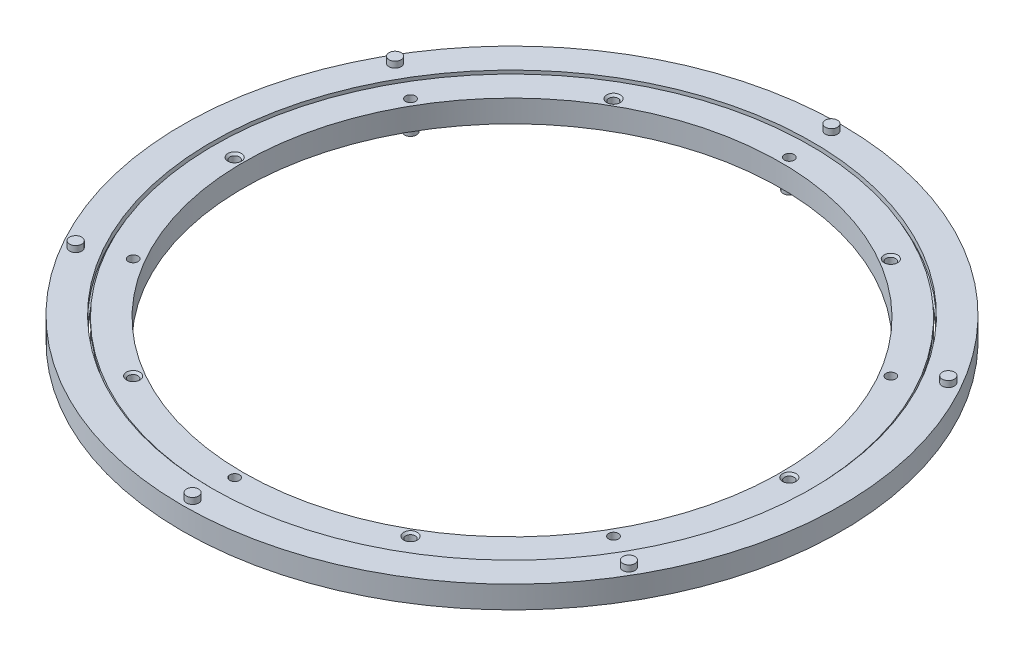
SolidWorks part; units mm, degrees
ref_plane "Front Plane" through (0, 0, 0) normal (0, 0, 1) x (1, 0, 0)
ref_plane "Top Plane" through (0, 0, 0) normal (0, 1, 0) x (1, 0, 0)
ref_plane "Right Plane" through (0, 0, 0) normal (1, 0, 0) x (0, 0, -1)
sketch "Sketch1" plane through (0, 0, 0) normal (0, 1, 0) x (1, 0, 0)
  line L0 (0, 162.5) -> (0, -162.5) construction
  line L1 (-162.5, 0) -> (162.5, 0) construction
  line L2 (68.375, 118.429) -> (0, 0) construction
  circle A0 centre (0, 0) radius 132.5
  circle A1 centre (0, 0) radius 162.5
  circle A2 centre (0, 0) radius 157.5 construction
  circle A3 centre (0, 0) radius 136.75 construction
  circle A4 centre (0, 157.5) radius 3
  circle A5 centre (0, 157.5) radius 2.4
  circle A6 centre (0, 136.75) radius 2.4
  circle A7 centre (0, 136.75) radius 3
  circle A8 centre (136.399, 78.75) radius 2.4
  circle A9 centre (136.399, -78.75) radius 2.4
  circle A10 centre (0, -157.5) radius 2.4
  circle A11 centre (-136.399, -78.75) radius 2.4
  circle A12 centre (-136.399, 78.75) radius 2.4
  circle A17 centre (118.429, 68.375) radius 2.4
  circle A18 centre (118.429, -68.375) radius 2.4
  circle A19 centre (0, -136.75) radius 2.4
  circle A20 centre (-118.429, -68.375) radius 2.4
  circle A21 centre (-118.429, 68.375) radius 2.4
  circle A24 centre (68.375, 118.429) radius 2.35
  circle A25 centre (136.75, 0) radius 2.35
  circle A26 centre (68.375, -118.429) radius 2.35
  circle A27 centre (-68.375, -118.429) radius 2.35
  circle A52 centre (-136.75, 0) radius 2.35
  circle A53 centre (-68.375, 118.429) radius 2.35
  point P28 (69.55, 120.4641)
  point P36 (0, 0)
  point P38 (0, 132.5)
  point P39 (0, 159.9)
  point P51 (0, 0)
  point P52 (0, 160.5)
  point P61 (0, 0)
  point P62 (0, 134.35)
  point P63 (0, 133.75)
  dimension "ID" = 265
  dimension "OD" = 325
  dimension "Outer Ring Dia" = 315
  dimension "Inner Ring Dia" = 273.5
  dimension "Bumper Hole Dia" = 4.8
  dimension "Bumper Dia" = 6
  dimension "Mounting Hole Dia" = 4.7
  dimension "D4" = 30
  dimension "No. Outside Bumpers" = 6
  dimension "No. Inside Bumpers" = 6
  dimension "No. Mounting Holes" = 6
sketch "Sketch2" plane through (0, 0, 0) normal (1, 0, 0) x (0, 0, -1)
  line L0 (147.5, 6) -> (147.5, -6) construction
  line L1 (132.5, -6) -> (132.5, 5)
  line L2 (132.5, 5) -> (147, 5)
  line L4 (147, -6) -> (132.5, -6)
  line L5 (162.5, 6) -> (148, 6)
  line L7 (148, -5) -> (162.5, -5)
  line L8 (162.5, -5) -> (162.5, 6)
  line L9 (147, 5) -> (147, -6)
  line L10 (134.35, 0.5) -> (136.75, 0.5)
  line L12 (148, 6) -> (148, -5)
  line L13 (132.5, 5) -> (162.5, -5) construction
  line L14 (162.5, 0) -> (-162.5, 0) construction
  line L15 (0, 6) -> (0, -6) construction
  line L16 (157.5, -5) -> (157.5, 9) construction
  line L18 (136.75, 5) -> (136.75, -9) construction
  line L19 (157.5, 9) -> (160.5, 9)
  line L20 (160.5, 9) -> (160.5, 6)
  line L21 (159.9, 6) -> (159.9, -0.5)
  line L22 (159.9, -0.5) -> (157.5, -0.5)
  line L23 (136.75, -9) -> (133.75, -9)
  line L24 (133.75, -9) -> (133.75, -6)
  line L25 (134.35, -6) -> (134.35, 5)
  line L27 (134.35, -6) -> (136.75, -6)
  circle A0 centre (147.5, 0) radius 3.25
  dimension "D4" = 6.5
  dimension "OA Height" = 12
  dimension "D3" = 1
  dimension "D5" = 6.5
  dimension "Bumper Height" = 3
  dimension "D8" = 3
  dimension "D1" = 1
  dimension "D2" = 6.5
sketch "Sketch4" plane through (0, 0, 0) normal (1, 0, 0) x (0, 0, -1)
  line L0 (147, 5) -> (147, -6) construction
  line L1 (132.5, 5) -> (147, 5) construction
  line L2 (132.5, -6) -> (132.5, 5) construction
  line L3 (147, -6) -> (132.5, -6) construction
  line L4 (147, 5) -> (147, 3.2113)
  line L5 (132.5, 5) -> (147, 5)
  line L6 (132.5, -6) -> (132.5, 5)
  line L7 (147, -6) -> (132.5, -6)
  line L8 (162.5, -5) -> (162.5, 6) construction
  line L9 (148, -5) -> (162.5, -5) construction
  line L10 (148, 6) -> (148, -5) construction
  line L11 (162.5, 6) -> (148, 6) construction
  line L12 (162.5, -5) -> (162.5, 6)
  line L13 (148, -5) -> (162.5, -5)
  line L14 (148, 6) -> (148, 3.2113)
  line L15 (162.5, 6) -> (148, 6)
  line L16 (148, -3.2113) -> (148, -5)
  line L17 (147, -3.2113) -> (147, -6)
  circle A0 centre (147.5, 0) radius 3.25 construction
  arc A1 (147, 3.2113) -> (147, -3.2113) centre (147.5, 0) ccw
  arc A2 (148, -3.2113) -> (148, 3.2113) centre (147.5, 0) ccw
revolve "Revolve1" add sketch "Sketch4" angle 360 about L15
sketch "Sketch6" plane through (0, 0, 0) normal (0, 1, 0) x (1, 0, 0)
  circle A0 centre (68.375, 118.429) radius 2.35 construction
  circle A1 centre (68.375, 118.429) radius 2.35
extrude "Cut-Extrude2" cut sketch "Sketch6" against normal through all both and the other way through all
chamfer "Chamfer1" distance 1 angle 45 1 edges at (68.375, 5, -120.779)
pattern_circular "CirPattern1" count 6 over 360 about axis through (0, 6, 0) along (0, -1, 0) of "Cut-Extrude2", "Chamfer1"
sketch "Sketch7" plane through (0, 6, 0) normal (0, 1, 0) x (1, 0, 0)
  circle A0 centre (0, 157.5) radius 2.4 construction
  circle A1 centre (0, 157.5) radius 2.4
extrude "Cut-Extrude3" cut sketch "Sketch7" against normal up to vertex (6.5 mm away) up to point (0, -0.5, -159.9)
pattern_circular "CirPattern2" count 6 over 360 about axis through (0, 0, 0) along (0, 1, 0) of "Cut-Extrude3"
sketch "Sketch8" plane through (0, 5, 0) normal (0, 1, 0) x (1, 0, 0)
  circle A0 centre (0, 136.75) radius 2.4 construction
  circle A1 centre (0, 136.75) radius 2.4
extrude "Cut-Extrude4" cut sketch "Sketch8" against normal through all
pattern_circular "CirPattern3" count 6 over 360 about axis through (0, 0, 0) along (0, 1, 0) of "Cut-Extrude4"
sketch "Sketch9" plane through (0, 0, 0) normal (1, 0, 0) x (0, 0, -1)
  line L0 (157.5, -5) -> (157.5, 9) construction
  line L1 (157.5, 9) -> (160.5, 9) construction
  line L2 (160.5, 9) -> (160.5, 6) construction
  line L3 (162.5, 6) -> (148, 6) construction
  line L4 (159.9, 6) -> (159.9, -0.5) construction
  line L6 (157.5, -0.5) -> (157.5, 9)
  line L7 (157.5, 9) -> (160.5, 9)
  line L8 (160.5, 9) -> (160.5, 6)
  line L9 (160.5, 6) -> (159.9, 6)
  line L10 (159.9, 6) -> (159.9, -0.5)
  line L12 (159.9, -0.5) -> (157.5, -0.5) construction
  line L13 (159.9, -0.5) -> (157.5, -0.5)
revolve "Revolve2" add sketch "Sketch9" angle 360 about L16
pattern_circular "CirPattern4" count 6 over 360 about axis through (0, 0, 0) along (0, 1, 0) of bodies 113
sketch "Sketch10" plane through (0, 0, 0) normal (1, 0, 0) x (0, 0, -1)
  line L2 (147, -6) -> (132.5, -6) construction
  line L3 (133.75, -9) -> (133.75, -6) construction
  line L4 (136.75, -9) -> (133.75, -9) construction
  line L7 (134.35, -6) -> (133.75, -6)
  line L8 (133.75, -9) -> (133.75, -6)
  line L9 (136.75, -9) -> (133.75, -9)
  line L10 (136.75, 5) -> (136.75, -9) construction
  line L11 (136.75, 0.5) -> (136.75, -9)
  line L12 (134.35, 0.5) -> (136.75, 0.5) construction
  line L13 (134.35, -6) -> (134.35, 5) construction
  line L14 (134.35, 0.5) -> (136.75, 0.5)
  line L15 (134.35, -6) -> (134.35, 0.5)
revolve "Revolve3" add sketch "Sketch10" angle 360 about L18
pattern_circular "CirPattern5" count 6 over 360 about axis through (0, 0, 0) along (0, 1, 0) of bodies 114
sketch "Drawing Ref" plane through (0, 0, 0) normal (1, 0, 0) x (0, 0, -1)
  line L0 (0, 6) -> (0, -6) construction
  line L1 (0, 6) -> (0, -6) construction
  line L2 (132.5, 6) -> (132.5, -5)
  line L3 (148, -5) -> (162.5, -5) construction
  line L4 (162.5, 6) -> (148, 6) construction
  line L5 (132.5, -6) -> (132.5, 5) construction
  line L6 (162.5, 6) -> (162.5, -6) construction
  line L7 (147, -6) -> (132.5, -6) construction
  line L8 (-132.5, 6) -> (-132.5, -5)
  line L9 (-162.5, 6) -> (-162.5, -6) construction
equation "\"D4@Sketch1\"=360/(\"No. Inside Bumpers@Sketch1\"*2)"
equation "\"D1@CirPattern1\"=\"No. Mounting Holes@Sketch1\""
equation "\"D8@Sketch2\" = \"Bumper Height@Sketch2\""
equation "\"D1@CirPattern2\"=\"No. Outside Bumpers@Sketch1\""
equation "\"D1@CirPattern3\"=\"No. Inside Bumpers@Sketch1\""
equation "\"D1@CirPattern4\"=\"No. Outside Bumpers@Sketch1\""
equation "\"D1@CirPattern5\"=\"No. Inside Bumpers@Sketch1\""
equation "\"D2@Sketch2\"=\"D5@Sketch2\""
